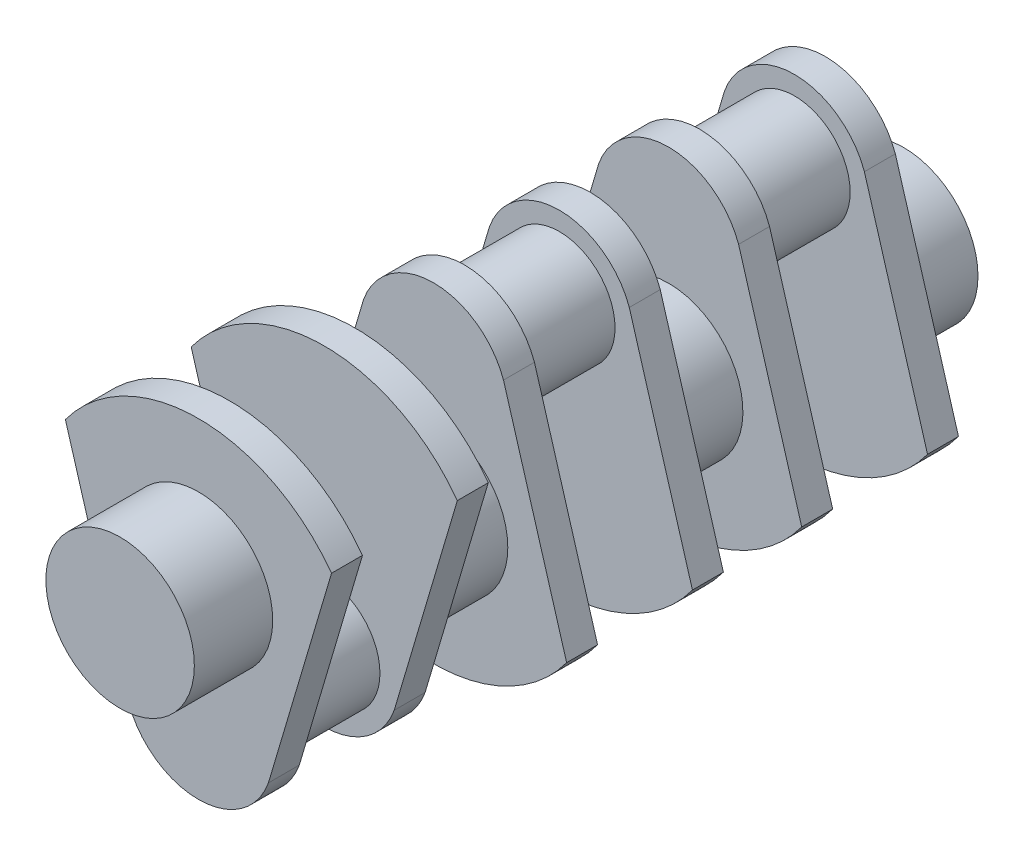
SolidWorks part; units mm, degrees
ref_plane "Front Plane" through (0, 0, 0) normal (0, 0, 1) x (1, 0, 0)
ref_plane "Top Plane" through (0, 0, 0) normal (0, 1, 0) x (1, 0, 0)
ref_plane "Right Plane" through (0, 0, 0) normal (1, 0, 0) x (0, 0, -1)
sketch "Sketch2" plane through (0, 0, 0) normal (0, 0, 1) x (1, 0, 0)
  line L0 (0, 782.014) -> (0, -1453.186) construction
  line L1 (-1715.8681, 50.6085) -> (2096.6365, 50.6085) construction
  line L2 (-1639.0739, 865.4389) -> (-861.3517, -1760.1072)
  line L3 (1639.0739, 865.4389) -> (861.3517, -1760.1072)
  circle A0 centre (0, -1453.186) radius 914.4
  arc A1 (-1639.0739, 865.4389) -> (1639.0739, 865.4389) centre (0, -335.586) cw
  dimension "D1" = 1828.8
  dimension "D3" = 2032
  dimension "D2" = 33
  dimension "D4" = 1117.6
extrude "Boss-Extrude1" add sketch "Sketch2" along normal blind 381 contours A1 L2 A0 L3 | L2 A0 L3
sketch "Sketch3" plane through (0, 0, 0) normal (0, 0, -1) x (-1, 0, 0)
  circle A0 centre (0, -1453.186) radius 685.8
  dimension "D1" = 1371.6
extrude "Boss-Extrude2" add sketch "Sketch3" along normal blind 1168.4
sketch "Sketch4" plane through (0, 0, 381) normal (0, 0, 1) x (1, 0, 0)
  circle A0 centre (0, 0) radius 914.4
  dimension "D1" = 1828.8
ref_plane "Plane3" through (0, 0, -584.2) normal (0, 0, -1) x (-1, 0, 0)
ref_plane "Plane9" through (0, 0, -584.2) normal (0, 0, -1) x (-1, 0, 0)
mirror "Mirror9" about plane through (0, 0, -584.2) normal (0, 0, -1) of bodies 102
extrude "Boss-Extrude5" add sketch "Sketch4" along normal blind 965.2
sketch "Sketch6" plane through (0, 0, -1549.4) normal (0, 0, -1) x (-1, 0, 0)
  circle A0 centre (0, 0) radius 914.4
  dimension "D1" = 1828.8
ref_plane "Plane11" through (0, 0, -2032) normal (0, 0, -1) x (-1, 0, 0)
mirror "Mirror14" about plane through (0, 0, -2032) normal (0, 0, -1) of bodies 120
move or copy body "Body-Move/Copy6" bodies to move or copy 124 copy no rotation origin (0, -335.586, -3962.4) rotation axis (1, 0, 0) rotation angle 180
move or copy body "Body-Move/Copy7" bodies to move or copy 125 copy no translate (0, 0, 965.2)
ref_plane "Plane12" through (0, 0, -4927.6) normal (0, 0, -1) x (-1, 0, 0)
mirror "Mirror16" about plane through (0, 0, -4927.6) normal (0, 0, -1) of bodies 126
sketch "Sketch7" plane through (0, 0, -4445) normal (0, 0, -1) x (-1, 0, 0)
  circle A0 centre (0, -671.172) radius 914.4
extrude "Boss-Extrude7" add sketch "Sketch7" along normal blind 965.2
